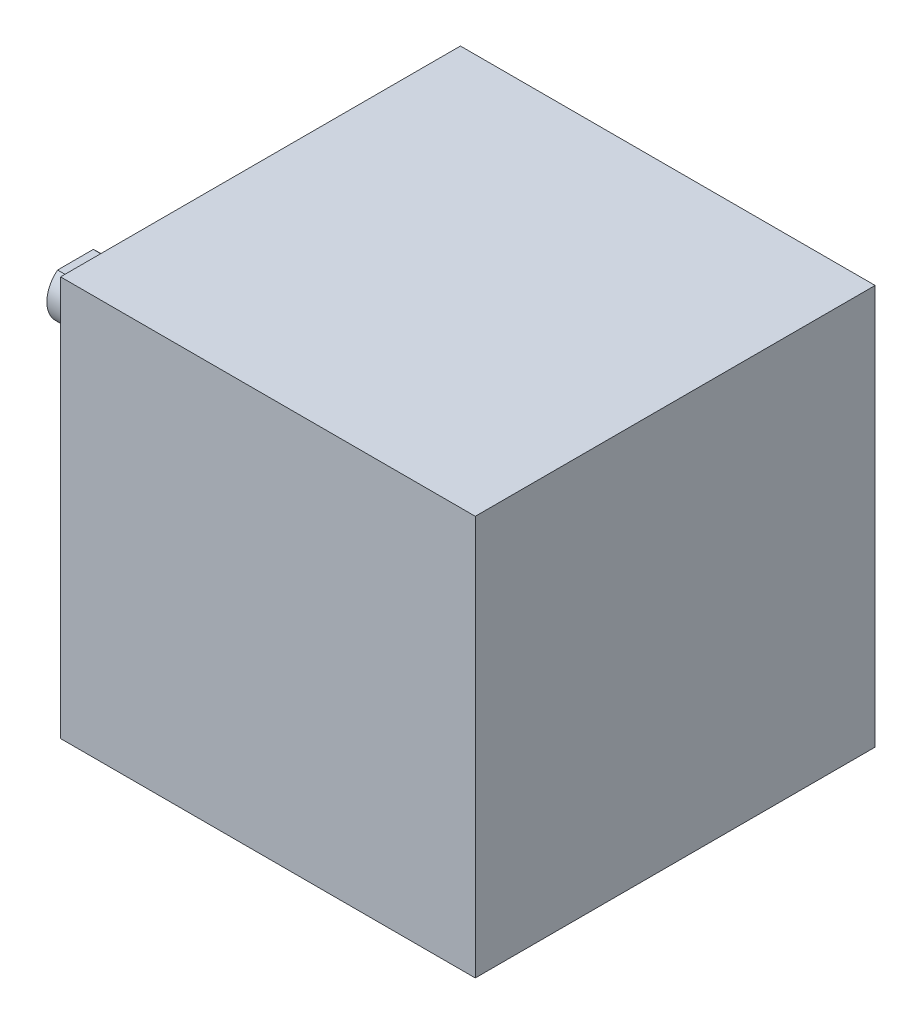
SolidWorks part; units mm, degrees
ref_plane "Front Plane" through (0, 0, 0) normal (0, 0, 1) x (1, 0, 0)
ref_plane "Top Plane" through (0, 0, 0) normal (0, 1, 0) x (1, 0, 0)
ref_plane "Right Plane" through (0, 0, 0) normal (1, 0, 0) x (0, 0, -1)
sketch "Sketch1" plane through (0, 0, 0) normal (1, 0, 0) x (0, 0, -1)
  line L1 (0, 0) -> (-35, 0)
  line L2 (0, 0) -> (0, -35)
  line L3 (0, -35) -> (-35, -35)
  line L4 (-35, 0) -> (-35, -35)
extrude "Boss-Extrude1" add sketch "Sketch1" along normal blind 36.3
sketch "Sketch2" plane through (0, 0, 0) normal (-1, 0, 0) x (0, 0, 1)
  circle A0 centre (17.5, -17.5) radius 11
extrude "Boss-Extrude2" add sketch "Sketch2" along normal blind 2
sketch "Sketch3" plane through (-2, 0, 0) normal (-1, 0, 0) x (0, 0, 1)
  line L1 (17.5, -15.55) -> (19.0644, -15.55)
  line L2 (17.5, -15.55) -> (15.9356, -15.55)
  arc A0 (15.9356, -15.55) -> (19.0644, -15.55) centre (17.5, -17.5) ccw
  point P6 (20, -15.55)
extrude "Boss-Extrude4" add sketch "Sketch3" along normal blind 14.2
